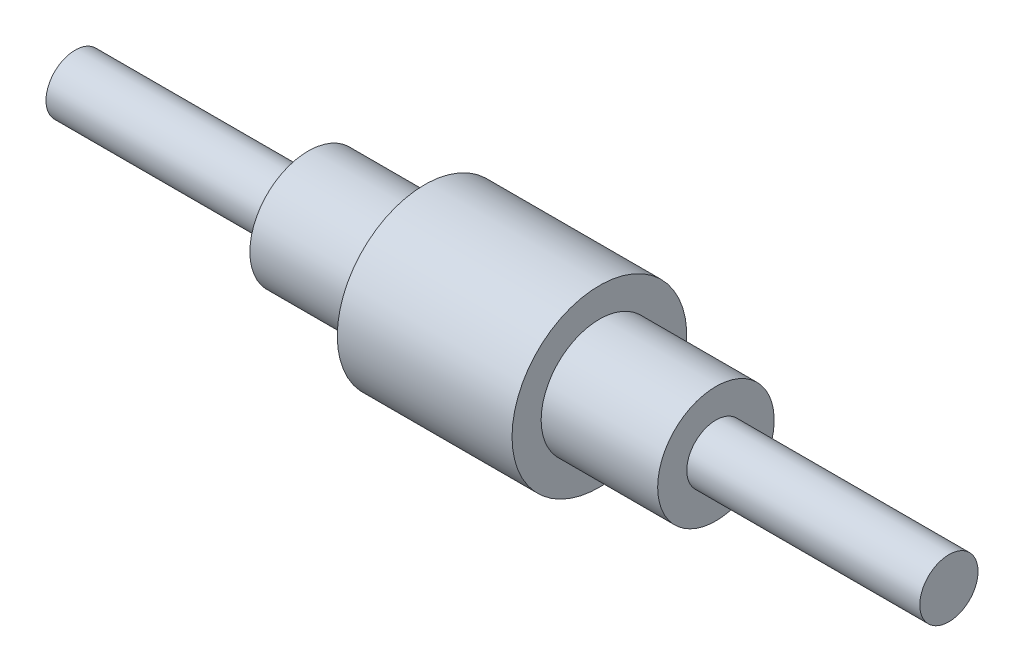
SolidWorks part; units mm, degrees
ref_plane "Front Plane" through (0, 0, 0) normal (0, 0, 1) x (1, 0, 0)
ref_plane "Top Plane" through (0, 0, 0) normal (0, 1, 0) x (1, 0, 0)
ref_plane "Right Plane" through (0, 0, 0) normal (1, 0, 0) x (0, 0, -1)
sketch "Sketch1" plane through (0, 0, 0) normal (0, 0, 1) x (1, 0, 0)
  line L0 (0, 0) -> (19.9494, 0) construction
  line L1 (0, 0) -> (0, -10)
  line L2 (0, -10) -> (80, -10)
  line L3 (80, -10) -> (80, -20)
  line L4 (80, -20) -> (120, -20)
  line L5 (120, -20) -> (120, -30)
  line L6 (120, -30) -> (180, -30)
  line L7 (180, -30) -> (180, -20)
  line L8 (180, -20) -> (220, -20)
  line L9 (220, -20) -> (220, -10)
  line L10 (220, -10) -> (300, -10)
  line L11 (300, -10) -> (300, 0)
  line L12 (0, 0) -> (300, 0)
revolve "Revolve1" add sketch "Sketch1" angle 360 about L0
